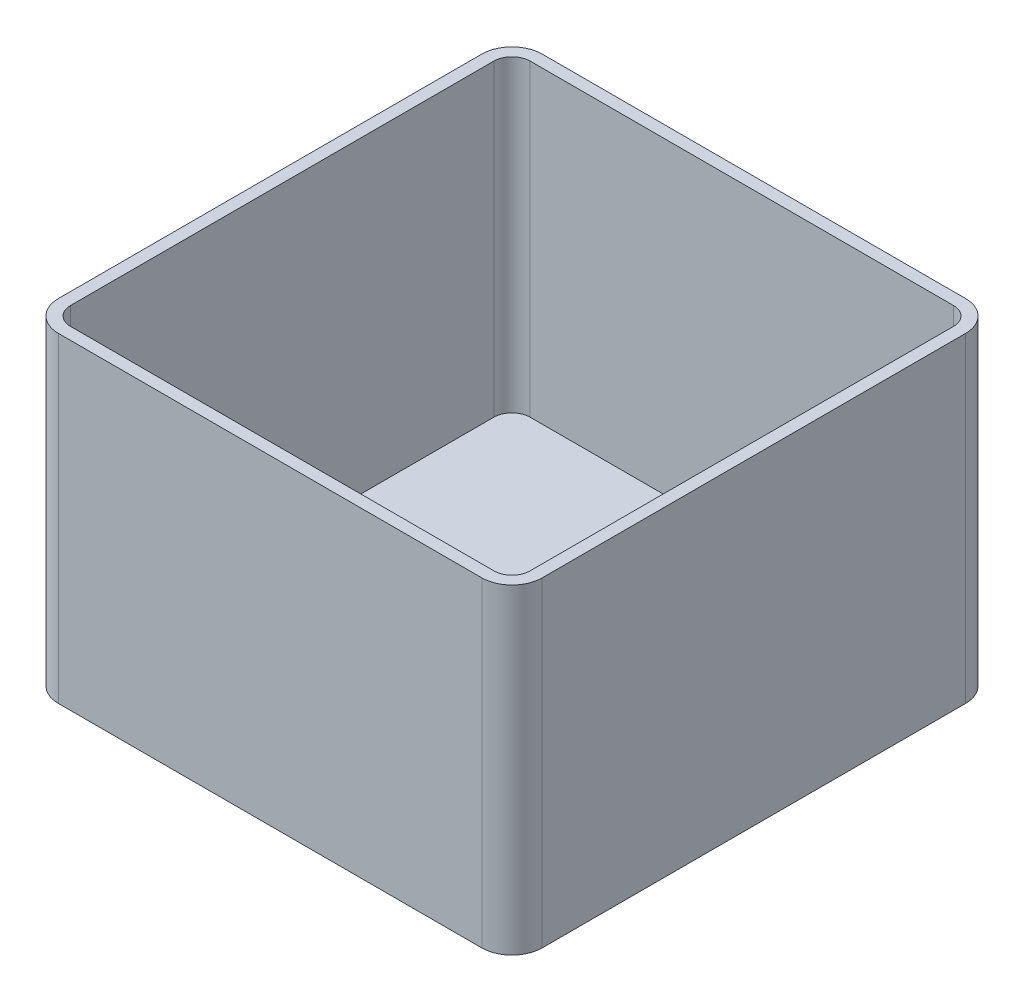
SolidWorks part; units mm, degrees
ref_plane "Face" through (0, 0, 0) normal (0, 0, 1) x (1, 0, 0)
ref_plane "Dessus" through (0, 0, 0) normal (0, 1, 0) x (1, 0, 0)
ref_plane "Droite" through (0, 0, 0) normal (1, 0, 0) x (0, 0, -1)
sketch "Esquisse1" plane through (0, 0, 0) normal (0, 1, 0) x (1, 0, 0)
  line L1 (0, 0) -> (80, 0)
  line L2 (0, 0) -> (0, 80)
  line L3 (0, 80) -> (80, 80)
  line L4 (80, 0) -> (80, 80)
  dimension "D1" = 80
  dimension "D2" = 80
extrude "Extrusion1" add sketch "Esquisse1" along normal blind 53
fillet "Congé1" radius 5 4 edges at (0, 26.5, 0) (0, 26.5, -80) (80, 26.5, -80) (80, 26.5, 0)
shell "Coque1" thickness 2
